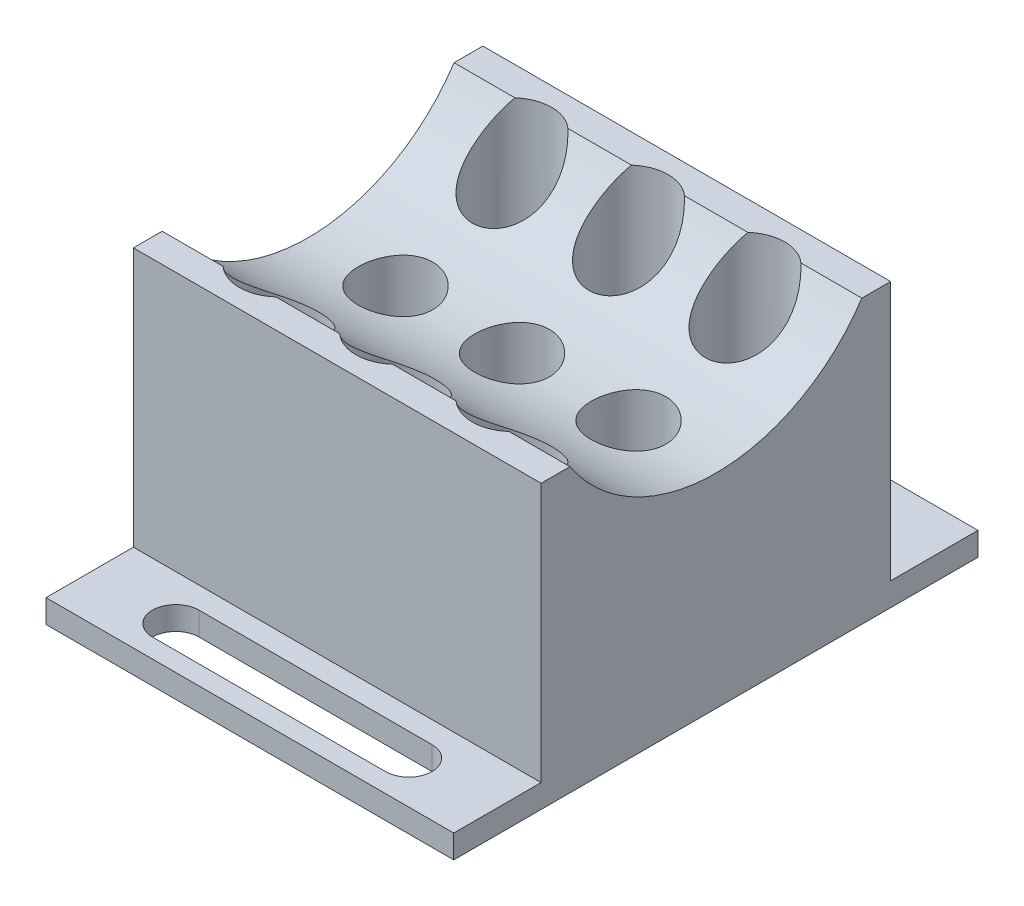
SolidWorks part; units mm, degrees
ref_plane "Front Plane" through (0, 0, 0) normal (0, 0, 1) x (1, 0, 0)
ref_plane "Top Plane" through (0, 0, 0) normal (0, 1, 0) x (1, 0, 0)
ref_plane "Right Plane" through (0, 0, 0) normal (1, 0, 0) x (0, 0, -1)
sketch "Sketch8" plane through (0, 0, 0) normal (0, 1, 0) x (1, 0, 0)
  line L1 (-17.5, -15) -> (17.5, -15)
  line L2 (-17.5, -15) -> (-17.5, 15)
  line L3 (-17.5, 15) -> (17.5, 15)
  line L4 (17.5, -15) -> (17.5, 15)
  line L5 (-17.5, -15) -> (17.5, 15) construction
  line L6 (-17.5, 15) -> (17.5, -15) construction
  point P0 (0, 0)
extrude "Boss-Extrude7" add sketch "Sketch8" along normal blind 80
sketch "Sketch10" plane through (0, 0, 0) normal (1, 0, 0) x (0, 0, -1)
  line L0 (0, 0) -> (0, 40) construction
  circle A0 centre (0, 40) radius 15
extrude "Cut-Extrude3" cut sketch "Sketch10" against normal through all and the other way through all
sketch "Sketch11" plane through (0, 0, 0) normal (1, 0, 0) x (0, 0, -1)
  line L1 (19.1682, 48.25) -> (-19.1682, 48.25)
  line L2 (19.1682, 48.25) -> (19.1682, 31.75)
  line L3 (19.1682, 31.75) -> (-19.1682, 31.75)
  line L4 (-19.1682, 48.25) -> (-19.1682, 31.75)
  line L5 (19.1682, 48.25) -> (-19.1682, 31.75) construction
  line L6 (19.1682, 31.75) -> (-19.1682, 48.25) construction
  point P0 (0, 40)
extrude "Cut-Extrude4" cut sketch "Sketch11" against normal through all both and the other way through all
sketch "Sketch12" plane through (0, 0, 0) normal (1, 0, 0) x (0, 0, -1)
  line L1 (17.3515, 0) -> (-16.4734, 0)
  line L2 (17.3515, 0) -> (17.3515, 7.5)
  line L3 (17.3515, 7.5) -> (-16.4734, 7.5)
  line L4 (-16.4734, 0) -> (-16.4734, 7.5)
  point P4 (-19.4469, 14.0871)
  point P5 (0, 0)
  point P6 (-19.1684, 16.6731)
  point P7 (-16.3466, 18.6086)
  point P8 (-16.4734, 15.2453)
extrude "Cut-Extrude5" cut sketch "Sketch12" against normal through all both and the other way through all
sketch "Sketch13" plane through (0, 0, 0) normal (1, 0, 0) x (0, 0, -1)
  line L1 (-29.3401, 40.0643) -> (16.2017, 40.0643)
  line L2 (-29.3401, 40.0643) -> (-29.3401, 81.5521)
  line L3 (-29.3401, 81.5521) -> (16.2017, 81.5521)
  line L4 (16.2017, 40.0643) -> (16.2017, 81.5521)
extrude "Cut-Extrude6" cut sketch "Sketch13" against normal through all both and the other way through all
ref_plane "Plane3" through (0, 7.5, 0) normal (0, -1, 0) x (-1, 0, 0)
sketch "Sketch15" plane through (0, 7.5, 0) normal (0, -1, 0) x (-1, 0, 0)
  line L1 (17.5, -15) -> (-17.5, -15)
  line L2 (17.5, -15) -> (17.5, -22.5)
  line L3 (17.5, -22.5) -> (-17.5, -22.5)
  line L4 (-17.5, -15) -> (-17.5, -22.5)
  line L5 (17.5, 15) -> (-17.5, 15)
  line L6 (17.5, 15) -> (17.5, 22.5)
  line L7 (17.5, 22.5) -> (-17.5, 22.5)
  line L8 (-17.5, 15) -> (-17.5, 22.5)
extrude "Boss-Extrude9" add sketch "Sketch15" against normal blind 2
sketch "Sketch16" plane through (0, 7.5, 0) normal (0, -1, 0) x (-1, 0, 0)
  line L0 (17.5, -22.5) -> (-17.5, -15.227) construction
  line L1 (-17.5, 22.5) -> (-17.5, -22.5) construction
  line L2 (-17.5, -22.5) -> (17.5, -15.227) construction
  line L3 (17.5, 22.5) -> (17.5, -22.5) construction
  line L4 (10, -18.8635) -> (-10, -18.8635) construction
  line L5 (10, -20.8635) -> (-10, -20.8635)
  line L6 (10, -16.8635) -> (-10, -16.8635)
  line L7 (17.5, 22.5) -> (-17.5, 15.1069) construction
  line L8 (-17.5, 22.5) -> (17.5, 15.1069) construction
  line L9 (10, 18.8035) -> (-10, 18.8035) construction
  line L10 (10, 16.8035) -> (-10, 16.8035)
  line L11 (10, 20.8035) -> (-10, 20.8035)
  arc A0 (10, -20.8635) -> (10, -16.8635) centre (10, -18.8635) ccw
  arc A1 (-10, -16.8635) -> (-10, -20.8635) centre (-10, -18.8635) ccw
  arc A2 (10, 16.8035) -> (10, 20.8035) centre (10, 18.8035) ccw
  arc A3 (-10, 20.8035) -> (-10, 16.8035) centre (-10, 18.8035) ccw
  point P12 (0, -18.8635)
  point P25 (0, 18.8035)
extrude "Cut-Extrude7" cut sketch "Sketch16" against normal blind 2
ref_plane "Plane5" through (0, 25, 0) normal (0, 1, 0) x (1, 0, 0)
sketch "Sketch18" plane through (0, 25, 0) normal (0, 1, 0) x (1, 0, 0)
  circle A0 centre (0, 0) radius 3.2
  circle A1 centre (10, 0) radius 3.2
  circle A2 centre (-10, 0) radius 3.2
  dimension "D1" = 2
  dimension "D2" = 2
extrude "Cut-Extrude10" cut sketch "Sketch18" against normal blind 6.4 and the other way through all
sketch "Sketch19" plane through (0, 25, 0) normal (0, 1, 0) x (1, 0, 0)
  line L0 (-10, 0) -> (-10, -10) construction
  circle A0 centre (-10, -10) radius 3.4
  circle A1 centre (0, -10) radius 3.4
  circle A2 centre (10, -10) radius 3.4
  circle A3 centre (-10, 10) radius 3.4
  circle A4 centre (0, 10) radius 3.4
  circle A5 centre (10, 10) radius 3.4
  dimension "D1" = 3
  dimension "D2" = 2
ref_plane "Plane6" through (-10, 0, 0) normal (-1, 0, 0) x (0, 0, 1)
sketch "Sketch20" plane through (-10, 0, 0) normal (-1, 0, 0) x (0, 0, 1)
  line L0 (10, 25) -> (6.6, 25) construction
  line L1 (0, 25) -> (10, 25) construction
  line L2 (6.6, 25) -> (6.6, 27.5032) construction
extrude "Cut-Extrude11" cut sketch "Sketch19" along normal up to next and the other way blind 4.9
